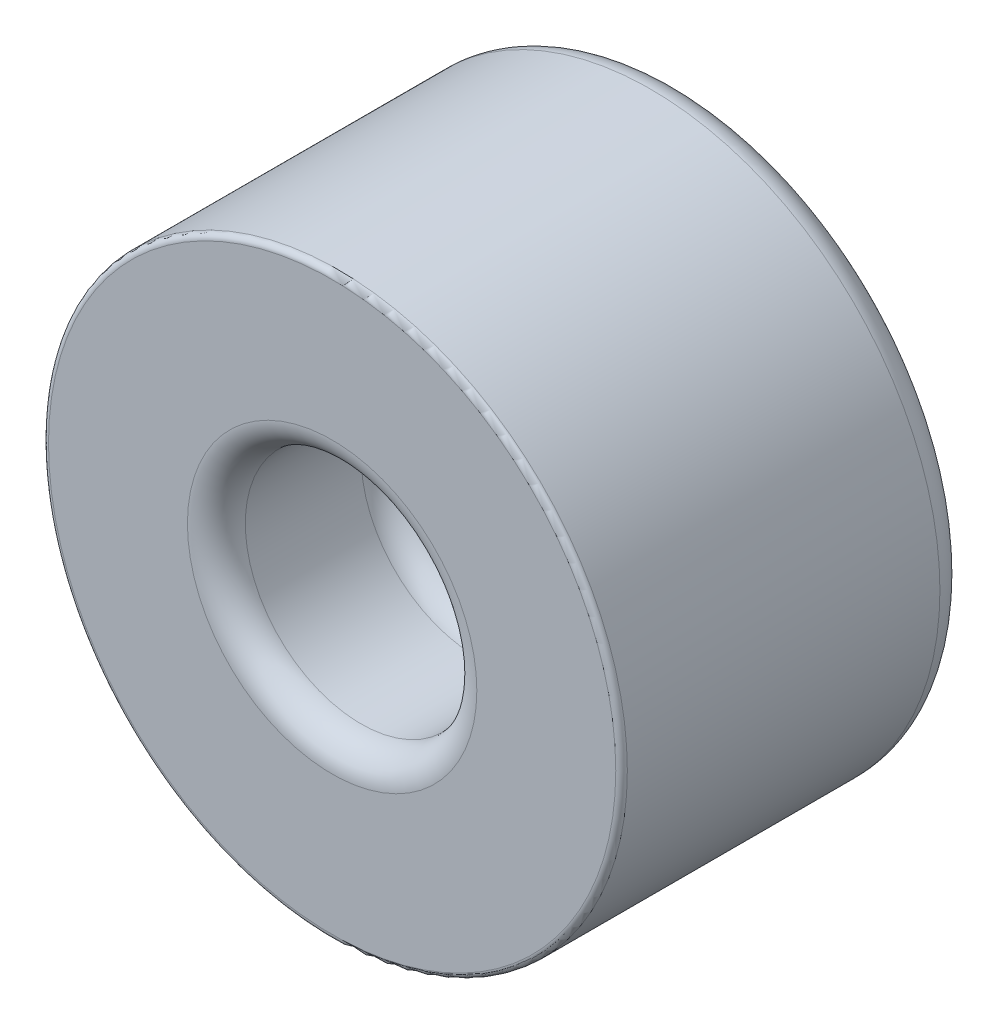
SolidWorks part; units mm, degrees
ref_plane "Piano frontale" through (0, 0, 0) normal (0, 0, 1) x (1, 0, 0)
ref_plane "Piano superiore" through (0, 0, 0) normal (0, 1, 0) x (1, 0, 0)
ref_plane "Piano destro" through (0, 0, 0) normal (1, 0, 0) x (0, 0, -1)
sketch "Schizzo1" plane through (0, 0, 0) normal (0, 0, 1) x (1, 0, 0)
  circle A0 centre (0, 0) radius 5
extrude "Estrusione-Estrusione1" add sketch "Schizzo1" along normal blind 6
sketch "Schizzo2" plane through (0, 0, 6) normal (0, 0, 1) x (1, 0, 0)
  circle A0 centre (0, 0) radius 2
extrude "Taglio-Estrusione1" cut sketch "Schizzo2" against normal blind 3
fillet "Raccordo1" radius 0.5 3 edges at (5, 0, 0) (2, 0, 6) (2, 0, 3)
fillet "Raccordo2" radius 0.1 1 edges at (5, 0, 6)
